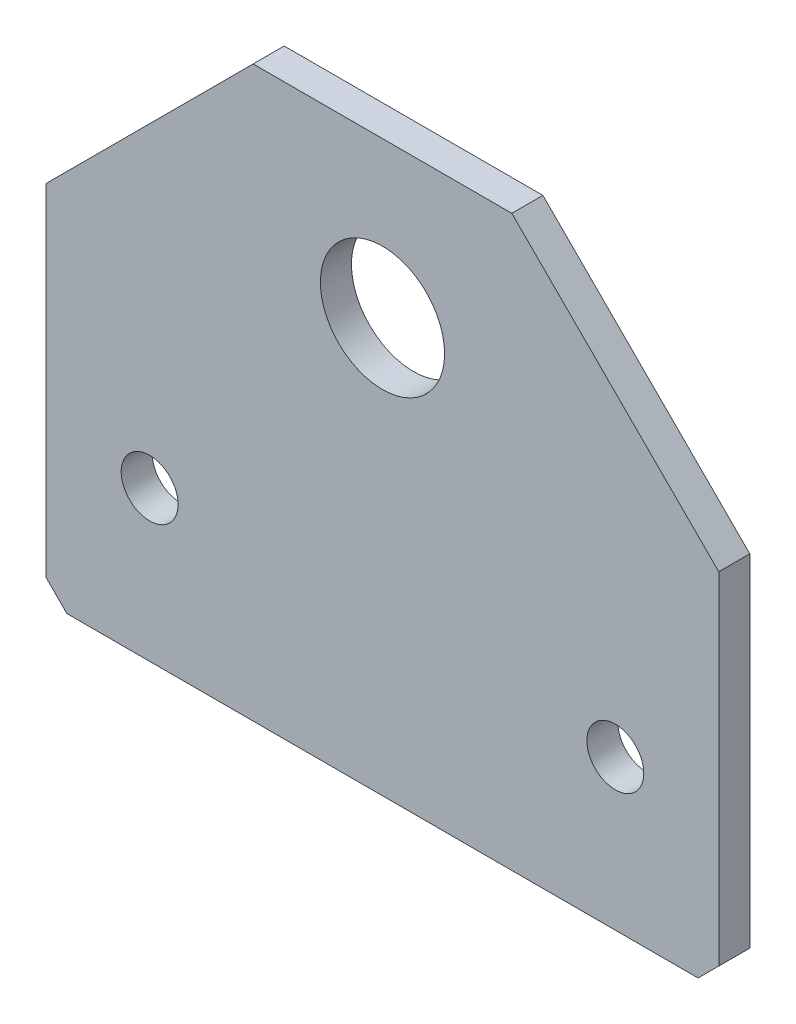
SolidWorks part; units mm, degrees
ref_plane "Front" through (0, 0, 0) normal (0, 0, 1) x (1, 0, 0)
ref_plane "Top" through (0, 0, 0) normal (0, 1, 0) x (1, 0, 0)
ref_plane "Right" through (0, 0, 0) normal (1, 0, 0) x (0, 0, -1)
sketch "Sketch1" plane through (0, 0, 0) normal (0, 0, 1) x (1, 0, 0)
  line L0 (0, 58.8405) -> (0, -10.7319) construction
  line L1 (-12.5, 55) -> (-32.5, 35)
  line L2 (-30.5, 0) -> (30.5, 0)
  line L3 (-32.5, 2) -> (-32.5, 35)
  line L4 (-12.5, 55) -> (12.5, 55)
  line L5 (32.5, 2) -> (32.5, 35)
  line L6 (12.5, 55) -> (32.5, 35)
  line L7 (-32.5, 2) -> (-30.5, 0)
  line L8 (32.5, 2) -> (30.5, 0)
  dimension "D1" = 65
  dimension "D2" = 55
  dimension "D3" = 2
  dimension "D4" = 2
  dimension "D5" = 35
  dimension "D6" = 20
extrude "Boss-Extrude1" add sketch "Sketch1" along normal blind 3
sketch "Sketch2" plane through (0, 0, 0) normal (0, 0, 1) x (1, 0, 0)
  line L0 (-30.5, 0) -> (30.5, 0) construction
  circle A0 centre (0, 40) radius 6
  dimension "D1" = 12
  dimension "D2" = 40
extrude "Cut-Extrude1" cut sketch "Sketch2" along normal through all
hole_wizard "M5 Clearance Hole1" positions "Sketch4" profile "Sketch3" hole size "M5" standard "JIS" end condition through all
sketch "Sketch4" plane through (0, 0, 3) normal (0, 0, 1) x (1, 0, 0)
  line L0 (0, -1.8675) -> (0, 56.9389) construction
  line L2 (-36.0404, 14.5) -> (35.969, 14.5) construction
  circle A1 centre (0, 40) radius 6 construction
  point P1 (-22.5, 14.5)
  point P5 (22.5, 14.5)
  point P20 (0, 0)
  point P21 (0, 0)
  point P22 (0, 0)
  point P23 (0, 0)
  point P24 (0, 0)
  dimension "D3" = 25.5
  dimension "D2" = 45
sketch "Sketch3" plane through (-22.5, 14.5, 3) normal (1, 0, 0) x (0, -1, 0)
  line L0 (0, 0) -> (0, 3)
  line L1 (0, 3) -> (2.75, 3)
  line L2 (2.75, 3) -> (2.75, 0)
  line L5 (2.75, 0) -> (0, 0)
  line L11 (0, -6.35) -> (0, 107.95) construction
  dimension "通し穴の直径" = 5.5
  dimension "通し穴の深さ" = 3
